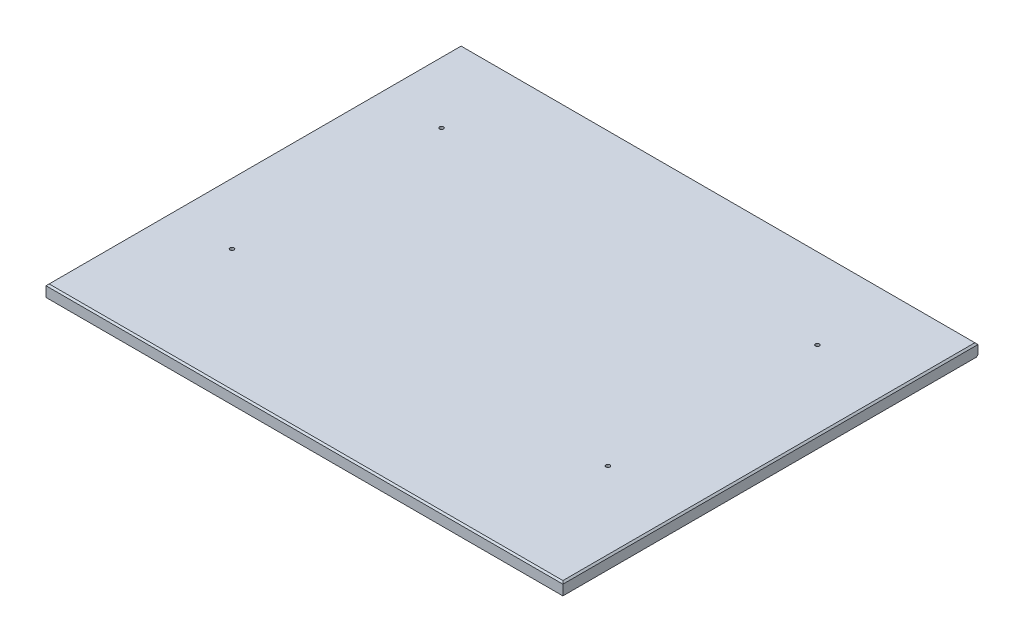
SolidWorks part; units mm, degrees
material "Oak"
ref_plane "Front Plane" through (0, 0, 0) normal (0, 0, 1) x (1, 0, 0)
ref_plane "Top Plane" through (0, 0, 0) normal (0, 1, 0) x (1, 0, 0)
ref_plane "Right Plane" through (0, 0, 0) normal (1, 0, 0) x (0, 0, -1)
sketch "Sketch1" plane through (0, 0, 0) normal (0, 1, 0) x (1, 0, 0)
  line L1 (0, 0) -> (838.2, 0)
  line L2 (0, 0) -> (0, 673.1)
  line L3 (0, 673.1) -> (838.2, 673.1)
  line L4 (838.2, 0) -> (838.2, 673.1)
  dimension "D1" = 673.1
  dimension "D2" = 838.2
extrude "Boss-Extrude1" add sketch "Sketch1" along normal blind 19.05
chamfer "Chamfer1" distance 2.54 angle 45 4 edges at (419.1, 19.05, -673.1) (838.2, 19.05, -336.55) (419.1, 19.05, 0) (0, 19.05, -336.55)
chamfer "Chamfer2" distance 2.54 angle 45 1 edges at (419.1, 0, -673.1)
sketch "Sketch2" plane through (0, 19.05, 0) normal (0, 1, 0) x (1, 0, 0)
  line L1 (101.6, 539.75) -> (711.2, 539.75) construction
  line L2 (101.6, 539.75) -> (101.6, 200.025) construction
  line L3 (101.6, 200.025) -> (711.2, 200.025) construction
  line L4 (711.2, 539.75) -> (711.2, 200.025) construction
  circle A1 centre (101.6, 539.75) radius 3.175
  circle A3 centre (101.6, 200.025) radius 3.175
  circle A5 centre (711.2, 539.75) radius 3.175
  circle A7 centre (711.2, 200.025) radius 3.175
  dimension "D1" = 6.35
  dimension "D2" = 609.6
  dimension "D3" = 339.725
  dimension "D4" = 200.025
  dimension "D5" = 101.6
extrude "Cut-Extrude1" cut sketch "Sketch2" against normal through all
